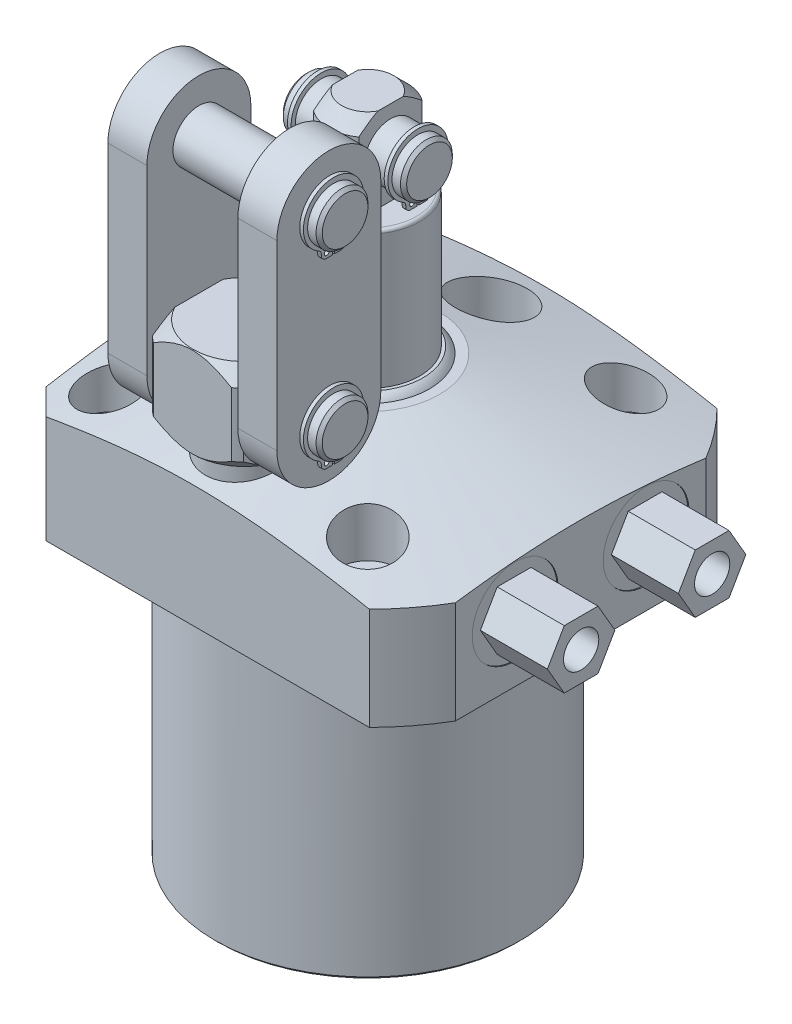
SolidWorks part; units mm, degrees
material "Alloy Steel"
ref_plane "Front Plane" through (0, 0, 0) normal (0, 0, 1) x (1, 0, 0)
ref_plane "Top Plane" through (0, 0, 0) normal (0, 1, 0) x (1, 0, 0)
ref_plane "Right Plane" through (0, 0, 0) normal (1, 0, 0) x (0, 0, -1)
sketch "Sketch28" plane through (0, 0, 0) normal (0, 0, 1) x (1, 0, 0)
  line L0 (0, 0) -> (0, 146.1857) construction
  line L1 (-17.4625, 36.4998) -> (-60.325, 25.0148)
  line L2 (-60.325, 25.0148) -> (-60.325, 0)
  line L3 (-60.325, 0) -> (-37.2999, 0)
  line L6 (-37.2999, 0) -> (-37.2999, -69.85)
  line L9 (-37.2999, -69.85) -> (0, -69.85)
  line L10 (0, -69.85) -> (0, 36.4998)
  line L11 (0, 36.4998) -> (-17.4625, 36.4998)
  dimension "D2" = 74.5998
  dimension "D3" = 69.85
  dimension "D5" = 120.65
  dimension "D6" = 15
  dimension "D7" = 34.925
  dimension "D8" = 36.4998
revolve "Revolve7" add sketch "Sketch28" angle 360 about L0
sketch "Sketch3" plane through (0, 36.4998, 0) normal (0, 1, 0) x (-1, 0, 0)
  line L0 (42.4688, -42.4688) -> (-51.9938, -42.4688)
  line L3 (-51.9938, 42.4688) -> (42.4688, 42.4688)
  line L4 (42.4688, -42.4688) -> (42.4688, 42.4688)
  line L5 (-51.9938, -42.4688) -> (-51.9938, 42.4688)
  line L6 (-29.7523, 0) -> (31.3525, 0) construction
  dimension "D1" = 84.9376
  dimension "D2" = 51.9938
  dimension "D5" = 42.4688
extrude "Cut-Extrude9" cut sketch "Sketch3" against normal up to next (106.3498 mm away) flip side to cut
chamfer "Chamfer8" distance 6.35 angle 45 2 edges at (-42.4688, 12.5429, -42.4688) (-42.4688, 12.5429, 42.4688)
chamfer "Chamfer5" distance 0.762 angle 45 1 edges at (0, -69.85, -37.2999)
hole_wizard "Hole1" positions "Sketch32" profile "Sketch31" legacy
sketch "Sketch32" plane through (0, 36.4998, 0) normal (0, 1, 0) x (-1, 0, 0)
  line L1 (0, 0) -> (-56.2722, 0) construction
  line L2 (0, 0) -> (0, 46.6984) construction
  point P11 (-31.496, -31.496)
  point P23 (-31.496, 31.496)
  point P25 (31.496, -31.496)
  point P26 (31.496, 31.496)
  dimension "D1" = 62.992
  dimension "D2" = 62.992
sketch "Sketch31" plane through (31.496, 36.4998, -31.496) normal (1, 0, 0) x (0, 0, 1)
  line L0 (0, 0) -> (0, 36.4998)
  line L1 (0, 36.4998) -> (4.3688, 36.4998)
  line L2 (4.3688, 36.4998) -> (4.3688, 17.4498)
  line L3 (4.3688, 17.4498) -> (7.1374, 17.4498)
  line L4 (7.1374, 17.4498) -> (7.1374, 0)
  line L5 (7.1374, 0) -> (0, 0)
  line L6 (0, 110) -> (0, -10) construction
  dimension "Diameter" = 8.7376
  dimension "Depth" = 36.4998
  dimension "C-Bore Diameter" = 14.2748
  dimension "C-Bore Depth" = 17.4498
sketch "Sketch34" plane through (0, 36.4998, 0) normal (0, 1, 0) x (1, 0, 0)
  line L0 (0, 0) -> (-28.6526, 0) construction
  circle A0 centre (0, 30.1498) radius 8.7503
  circle A1 centre (0, -30.1498) radius 8.7503
  circle A2 centre (0, 0) radius 30.1498 construction
  circle A3 centre (-30.1498, 0) radius 8.7503
  dimension "D1" = 17.5006
  dimension "D2" = 30.1498
extrude "Cut-Extrude10" cut sketch "Sketch34" against normal blind 19.05
ref_plane "Plane23" through (0, 15.875, 0) normal (0, -1, 0) x (1, 0, 0)
sketch "S2D0007" plane through (0, 15.875, 0) normal (0, -1, 0) x (1, 0, 0)
  line L0 (51.9938, -16.002) -> (51.9938, -26.4795)
  line L1 (51.9938, -26.4795) -> (51.7398, -26.4795)
  line L2 (51.7398, -26.4795) -> (51.7398, -22.2186)
  line L3 (51.7398, -22.2186) -> (49.6697, -21.7786)
  line L4 (49.6697, -21.7786) -> (48.8715, -20.9804)
  line L5 (48.8715, -20.9804) -> (37.7698, -20.9804)
  line L6 (37.7698, -20.9804) -> (34.7785, -16.002)
  line L7 (34.7785, -16.002) -> (51.9938, -16.002)
  line L8 (-11.7468, -16.002) -> (-12.1894, -16.002) construction
  line L10 (51.9938, -30.59) -> (51.9938, 30.59) construction
  dimension "D1" = 12.4333
  dimension "D2" = 59
  dimension "D3" = 9.9568
  dimension "D4" = 45
  dimension "D5" = 12
  dimension "D6" = 2.0701
  dimension "D7" = 0.254
  dimension "D8" = 20.955
  dimension "D9" = 16.002
  dimension "D10" = 13.97
revolve "Cut-Revolve2" cut sketch "S2D0007" angle 360 about L8
ref_plane "Plane24" through (0, 0, -16.002) normal (0, 0, 1) x (1, 0, 0)
sketch "Sketch6" plane through (0, 0, -16.002) normal (0, 0, 1) x (1, 0, 0)
  line L0 (42.8428, 0) -> (-36.1188, 0) construction
  line L1 (50.6793, 0) -> (50.6793, 1.4478)
  line L2 (50.6793, 1.4478) -> (47.6189, 1.4478)
  line L3 (42.8428, 0) -> (51.9938, 0) construction
  line L5 (45.0088, 0.5588) -> (46.1518, 0.5588)
  line L6 (45.0088, 0) -> (50.6793, 0)
  line L8 (45.0088, 0.5588) -> (45.0088, 0)
  line L9 (45.0088, -21.0492) -> (45.0088, 0.6686) construction
  arc A1 (46.1518, 0.5588) -> (47.6189, 1.4478) centre (45.0088, 4.1) ccw
  dimension "D8" = 3.7211
  dimension "D1" = 1.4478
  dimension "D2" = 45.0088
  dimension "D7" = 0.5588
  dimension "D9" = 11.3411
  dimension "D10" = 2.286
revolve "Cut-Revolve3" cut sketch "Sketch6" angle 360 about L9
sketch "Sketch38" plane through (51.7398, 0, 0) normal (1, 0, 0) x (0, 0, -1)
  line L1 (24.2436, 15.875) -> (20.1228, 23.0124)
  line L2 (20.1228, 23.0124) -> (11.8812, 23.0124)
  line L3 (11.8812, 23.0124) -> (7.7604, 15.875)
  line L4 (7.7604, 15.875) -> (11.8812, 8.7376)
  line L5 (11.8812, 8.7376) -> (20.1228, 8.7376)
  line L6 (20.1228, 8.7376) -> (24.2436, 15.875)
  circle A0 centre (16.002, 15.875) radius 7.1374 construction
  dimension "D1" = 14.2748
extrude "Extrude14" add sketch "Sketch38" along normal blind 16.383
hole_wizard "Hole2" positions "Sketch40" profile "Sketch39" legacy
sketch "Sketch40" plane through (68.1228, 0, 0) normal (1, 0, 0) x (0, 0, -1)
  circle A0 centre (16.002, 15.875) radius 10.4775 construction
  point P0 (16.002, 15.875)
sketch "Sketch39" plane through (68.1228, 15.875, -16.002) normal (0, 1, 0) x (0, 0, -1)
  line L0 (0, 0) -> (0, 6.7056)
  line L1 (0, 6.7056) -> (4.3053, 6.7056)
  line L2 (4.3053, 6.7056) -> (4.3053, 0)
  line L3 (4.3053, 0) -> (0, 0)
  line L4 (0, 110) -> (0, -10) construction
  dimension "Diameter" = 8.6106
  dimension "Depth" = 6.7056
mirror "Mirror6" about plane through (0, 0, 0) normal (0, 0, 1) of "Hole2", "Extrude14", "Cut-Revolve2", "Cut-Revolve3"
sketch "Sketch33" plane through (0, 0, -16.002) normal (0, 0, 1) x (1, 0, 0)
  line L0 (45.0088, 8.3297) -> (45.0088, -4.9597) construction
  line L1 (45.0088, 2.4904) -> (45.0088, -1.971) construction
  line L2 (39.3383, 1.4478) -> (50.6793, 1.4478) construction
  circle A0 centre (40.2272, 0.5842) radius 0.889
  dimension "D3" = 1.778
  dimension "D1" = 9.5631
  dimension "D2" = 0.8636
revolve "Revolve9" add sketch "Sketch33" angle 360 about L0
mirror "Mirror7" about plane through (0, 0, 0) normal (0, 0, 1) of bodies 147
sketch "Sketch12" plane through (0, 0, 0) normal (0, 0, -1) x (-1, 0, 0)
  line L0 (0, 36.4998) -> (0, 38.0238)
  line L1 (0, 38.0238) -> (13.462, 38.0238)
  line L2 (0, 36.4998) -> (15.0749, 36.4998)
  line L3 (0, 22.1056) -> (0, 27.6194) construction
  line L4 (17.4625, 36.4998) -> (-17.4625, 36.4998) construction
  arc A0 (15.0749, 36.4998) -> (13.462, 38.0238) centre (11.0966, 33.9049) ccw
  dimension "D1" = 4.7498
  dimension "D2" = 1.524
  dimension "D3" = 26.924
  dimension "D4" = 30.1498
revolve "Revolve2" add sketch "Sketch12" angle 360 about L3
ref_plane "Plane25" through (0, 0, 0) normal (1, 0, 0) x (0, 0, -1)
sketch "Sketch13" plane through (0, 0, 0) normal (0, 0, 1) x (1, 0, 0)
  line L0 (0, 38.0238) -> (0, 92.075)
  line L1 (0, 92.075) -> (6.35, 92.075)
  line L2 (6.35, 92.075) -> (9.525, 88.9)
  line L3 (9.525, 71.4502) -> (9.525, 88.9)
  line L4 (12.6937, 38.0238) -> (0, 38.0238)
  line L5 (0, 23.0264) -> (0, 64.961) construction
  line L6 (-6.0362, 82.55) -> (17.7755, 82.55) construction
  line L7 (13.462, 38.0238) -> (-13.462, 38.0238) construction
  line L8 (42.8428, 0) -> (-36.1188, 0) construction
  line L10 (9.525, 71.4502) -> (12.6937, 71.4502)
  line L11 (12.6937, 71.4502) -> (12.6937, 38.0238)
  dimension "D1" = 9.525
  dimension "D2" = 82.55
  dimension "D3" = 19.05
  dimension "D4" = 45
  dimension "D5" = 3.175
  dimension "D6" = 25.3873
  dimension "D7" = 20.6248
revolve "Revolve3" add sketch "Sketch13" angle 360 about L5
sketch "Sketch14" plane through (0, 92.075, 0) normal (0, 1, 0) x (-1, 0, 0)
  line L0 (-5.5499, -7.7411) -> (-5.5499, 7.7411)
  line L2 (5.5499, 7.7411) -> (5.5499, -7.7411)
  line L4 (0, 0) -> (0, 0.0001) construction
  line L5 (0, 34.2265) -> (0, -34.2265) construction
  circle A0 centre (0, 0) radius 9.525 construction
  arc A1 (-5.5499, 7.7411) -> (-5.5499, -7.7411) centre (0, 0) ccw
  arc A2 (5.5499, -7.7411) -> (5.5499, 7.7411) centre (0, 0) ccw
  dimension "D1" = 11.0998
extrude "Cut-Extrude7" cut sketch "Sketch14" against normal up to surface (20.6248 mm away) up to face at (0, 71.4502, -9.525)
fillet "Fillet4" radius 0.762 3 edges at (0, 71.4502, -12.6937) (0, 71.4502, 9.525) (0, 71.4502, -9.525)
sketch "Sketch29" plane through (0, 0, 0) normal (1, 0, 0) x (0, 0, -1)
  line L0 (-3.0856, 92.075) -> (-6.35, 92.075) construction
  circle A0 centre (0, 82.55) radius 6.3373
  dimension "D1" = 12.6746
  dimension "D2" = 9.525
extrude "Extrude11" add sketch "Sketch29" along normal mid plane 30.1498
sketch "Sketch16" plane through (15.0749, 52.3748, 0) normal (1, 0, 0) x (0, 0, -1)
  line L0 (0.2388, 24.2364) -> (0.2388, 21.4932)
  line L1 (2.982, 22.9316) -> (2.982, 22.687)
  line L2 (1.7882, 21.4932) -> (0.2388, 21.4932)
  line L3 (-2.982, 22.9316) -> (-2.982, 22.687)
  line L4 (-1.7882, 21.4932) -> (-0.2388, 21.4932)
  line L5 (-0.2388, 24.2364) -> (-0.2388, 21.4932)
  line L6 (0, -3.8062) -> (0, 3.1748) construction
  arc A0 (0.2388, 24.2364) -> (-0.2388, 24.2364) centre (0, 30.1752) ccw
  arc A1 (3.5934, 23.9737) -> (-3.5934, 23.9737) centre (0, 30.4038) ccw
  arc A2 (3.5934, 23.9737) -> (2.982, 22.9316) centre (4.1758, 22.9316) ccw
  arc A3 (1.7882, 21.4932) -> (2.982, 22.687) centre (1.7882, 22.687) ccw
  circle A4 centre (1.4326, 22.687) radius 0.5969
  arc A5 (-3.5934, 23.9737) -> (-2.982, 22.9316) centre (-4.1758, 22.9316) cw
  arc A6 (-1.7882, 21.4932) -> (-2.982, 22.687) centre (-1.7882, 22.687) cw
  circle A7 centre (-1.4326, 22.687) radius 0.5969
  circle A8 centre (0, 30.1752) radius 6.3373 construction
  dimension "D1" = 7.366
  dimension "D4" = 1.1938
  dimension "D6" = 1.1938
  dimension "D7" = 2.7432
  dimension "D8" = 5.9436
  dimension "D10" = 1.1938
  dimension "D11" = 1.1938
  dimension "D2" = 2.7432
  dimension "D3" = 0.2286
  dimension "D5" = 1.4326
  dimension "D9" = 0.4775
extrude "Extrude2" add sketch "Sketch16" against normal blind 0.889 from offset 2.8194
chamfer "Chamfer6" distance 0.762 angle 45 2 edges at (-15.0749, 82.55, -6.3373) (15.0749, 82.55, -6.3373)
mirror "Mirror2" about plane through (0, 0, 0) normal (1, 0, 0) of "Extrude2"
sketch "Sketch35" plane through (0, 0, 0) normal (1, 0, 0) x (0, 0, -1)
  line L0 (-30.1498, 43.5741) -> (-30.1498, 11.6793) construction
  line L1 (-30.1498, 17.4498) -> (-20.6248, 17.4498)
  line L2 (-20.6248, 17.4498) -> (-20.6248, 36.4998)
  line L3 (-20.6248, 36.4998) -> (-17.5768, 36.4998)
  line L4 (-14.2748, 39.8018) -> (-14.2748, 55.4228)
  line L5 (-17.5768, 58.7248) -> (-30.1498, 58.7248)
  line L6 (-30.1498, 58.7248) -> (-30.1498, 17.4498)
  line L8 (-14.2748, 55.4228) -> (-17.5768, 58.7248)
  line L9 (-17.5768, 36.4998) -> (-14.2748, 39.8018)
  line L10 (-42.4688, 0) -> (-30.59, 0) construction
  point P6 (-14.2748, 36.4998)
  point P7 (-14.2748, 58.7248)
  dimension "D2" = 19.05
  dimension "D3" = 31.75
  dimension "D4" = 41.275
  dimension "D5" = 22.225
  dimension "D6" = 30.1498
  dimension "D9" = 3.302
  dimension "D10" = 3.302
  dimension "D7" = 36.4998
revolve "Revolve10" add sketch "Sketch35" angle 360 about L0
sketch "Sketch36" plane through (0, 58.7248, 0) normal (0, 1, 0) x (1, 0, 0)
  line L0 (0, -30.1498) -> (30.1498, -30.1498) construction
  line L1 (-11.1125, -41.4868) -> (-11.1125, -18.8128)
  line L2 (-9.525, -42.8498) -> (9.525, -42.8498)
  line L3 (11.1125, -41.4868) -> (11.1125, -18.8128)
  line L4 (-9.525, -17.4498) -> (9.525, -17.4498)
  line L5 (0, -30.1498) -> (0, 0) construction
  line L6 (0, -34.2265) -> (0, 34.2265) construction
  circle A0 centre (0, -30.1498) radius 15.875 construction
  arc A2 (-9.525, -42.8498) -> (9.525, -42.8498) centre (0, -30.1498) ccw
  arc A3 (11.1125, -41.4868) -> (11.1125, -18.8128) centre (0, -30.1498) ccw
  arc A4 (-11.1125, -18.8128) -> (-11.1125, -41.4868) centre (0, -30.1498) ccw
  arc A5 (9.525, -17.4498) -> (-9.525, -17.4498) centre (0, -30.1498) ccw
  dimension "D1" = 25.4
  dimension "D2" = 22.225
extrude "Cut-Extrude11" cut sketch "Sketch36" against normal up to surface (22.225 mm away) up to face at (0, 36.4998, 42.7228)
sketch "Sketch30" plane through (0, 0, 0) normal (1, 0, 0) x (0, 0, -1)
  line L0 (-42.4688, 0) -> (42.4688, 0) construction
  circle A0 centre (-30.1498, 47.625) radius 6.3373
  dimension "D3" = 12.6746
  dimension "D1" = 47.625
  dimension "D2" = 30.1498
extrude "Extrude12" add sketch "Sketch30" along normal mid plane 49.1998
sketch "Sketch19" plane through (24.5999, 11.0998, 22.225) normal (1, 0, 0) x (0, 0, -1)
  line L0 (-7.686, 30.5864) -> (-7.686, 27.8432)
  line L1 (-4.9428, 29.2816) -> (-4.9428, 29.037)
  line L2 (-6.1366, 27.8432) -> (-7.686, 27.8432)
  line L3 (-10.9068, 29.2816) -> (-10.9068, 29.037)
  line L4 (-9.713, 27.8432) -> (-8.1636, 27.8432)
  line L5 (-8.1636, 30.5864) -> (-8.1636, 27.8432)
  line L6 (-7.9248, -5.3833) -> (-7.9248, 4.2478) construction
  arc A0 (-7.686, 30.5864) -> (-8.1636, 30.5864) centre (-7.9248, 36.5252) ccw
  arc A1 (-4.3314, 30.3237) -> (-11.5182, 30.3237) centre (-7.9248, 36.7538) ccw
  arc A2 (-4.3314, 30.3237) -> (-4.9428, 29.2816) centre (-3.749, 29.2816) ccw
  arc A3 (-6.1366, 27.8432) -> (-4.9428, 29.037) centre (-6.1366, 29.037) ccw
  circle A4 centre (-6.2535, 29.037) radius 0.5969
  arc A5 (-11.5182, 30.3237) -> (-10.9068, 29.2816) centre (-12.1006, 29.2816) cw
  arc A6 (-9.713, 27.8432) -> (-10.9068, 29.037) centre (-9.713, 29.037) cw
  circle A7 centre (-9.5961, 29.037) radius 0.5969
  circle A8 centre (-7.9248, 36.5252) radius 6.3373 construction
  dimension "D1" = 7.366
  dimension "D3" = 0.2286
  dimension "D4" = 1.1938
  dimension "D5" = 1.1938
  dimension "D6" = 1.1938
  dimension "D9" = 5.9436
  dimension "D2" = 2.7432
  dimension "D7" = 0.4775
  dimension "D8" = 2.7432
  dimension "D10" = 1.1938
  dimension "D11" = 1.4326
extrude "Extrude4" add sketch "Sketch19" against normal blind 0.889 from offset 2.8194
sketch "Sketch37" plane through (11.1125, 0, 0) normal (1, 0, 0) x (0, 0, -1)
  line L0 (-42.8498, 92.075) -> (-42.8498, 47.625)
  line L1 (-17.4498, 92.075) -> (-17.4498, 47.625)
  arc A0 (-17.4498, 92.075) -> (-42.8498, 92.075) centre (-30.1498, 92.075) ccw
  arc A1 (-42.8498, 47.625) -> (-17.4498, 47.625) centre (-30.1498, 47.625) ccw
  dimension "D1" = 25.4
  dimension "D2" = 44.45
  dimension "D3" = 31.6186
extrude "Extrude13" add sketch "Sketch37" along normal blind 9.525
mirror "Mirror3" about plane through (0, 0, 0) normal (1, 0, 0) of "Extrude4"
chamfer "Chamfer7" distance 0.762 angle 45 2 edges at (-24.5999, 47.625, 23.8125) (24.5999, 47.625, 23.8125)
pattern_linear "LPattern2" count 2 spacing 44.45 along (0, 1, 0) of "Extrude4", "Mirror3", "Chamfer7", "Extrude12"
mirror "Mirror8" about plane through (0, 0, 0) normal (1, 0, 0) of "Extrude13"
